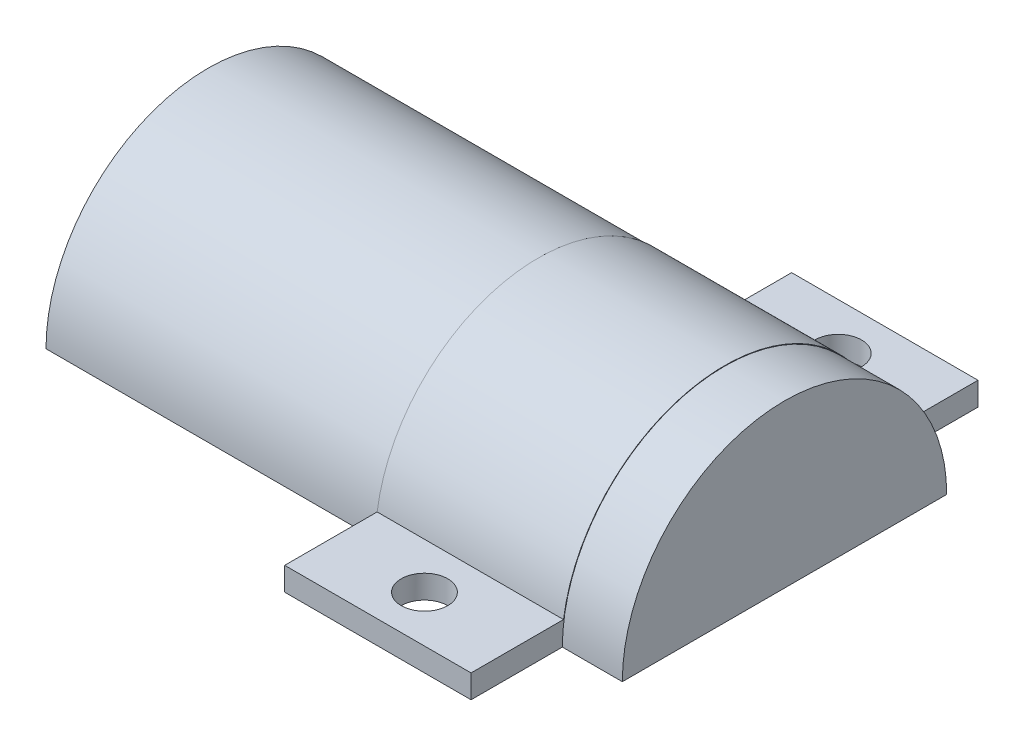
SolidWorks part; units mm, degrees
ref_plane "Front" through (0, 0, 0) normal (0, 0, 1) x (1, 0, 0)
ref_plane "Top" through (0, 0, 0) normal (0, 1, 0) x (1, 0, 0)
ref_plane "Right" through (0, 0, 0) normal (1, 0, 0) x (0, 0, -1)
sketch "Sketch1" plane through (0, 0, 0) normal (1, 0, 0) x (0, 0, -1)
  line L0 (-22.175, 0) -> (22.175, 0)
  line L1 (-22.175, 0) -> (-34.5465, 0)
  line L2 (-34.5465, 0) -> (-34.5465, 3.175)
  line L3 (-34.5465, 3.175) -> (-21.9465, 3.175)
  line L4 (0, 54.7215) -> (0, -65.0563) construction
  line L5 (22.175, 0) -> (34.5465, 0)
  line L6 (34.5465, 0) -> (34.5465, 3.175)
  line L7 (34.5465, 3.175) -> (21.9465, 3.175)
  circle A0 centre (0, 0) radius 19
  circle A1 centre (0, 0) radius 22.175
  dimension "D1" = 38
  dimension "D3" = 3.175
  dimension "D4" = 12.6
  dimension "D2" = 3.175
extrude "Boss-Extrude1" add sketch "Sketch1" along normal blind 25.4 contours A1 L3 L2 L1 | L4 A1 L0 A0 | A1 L4 A0 L0 | A1 L5 L6 L7
sketch "Sketch2" plane through (0, 3.175, 0) normal (0, 1, 0) x (1, 0, 0)
  line L0 (0, -34.5465) -> (0, -21.9465) construction
  line L2 (25.4, -34.5465) -> (0, -34.5465) construction
  circle A0 centre (12.7, -28.1965) radius 3.175
  dimension "D1" = 6.35
  dimension "D2" = 12.7
  dimension "D3" = 6.35
extrude "Cut-Extrude1" cut sketch "Sketch2" against normal blind 25.4
sketch "Sketch3" plane through (0, 3.175, 0) normal (0, 1, 0) x (1, 0, 0)
  line L0 (25.4, 34.5465) -> (25.4, 21.9465) construction
  line L1 (25.4, 34.5465) -> (0, 34.5465) construction
  circle A0 centre (12.7, 28.1965) radius 3.175
  dimension "D3" = 6.35
  dimension "D1" = 12.7
  dimension "D2" = 6.35
extrude "Cut-Extrude2" cut sketch "Sketch3" against normal blind 25.4
sketch "Sketch4" plane through (25.4, 0, 0) normal (1, 0, 0) x (0, 0, -1)
  line L0 (-19, 0) -> (-22.1047, 0)
  line L1 (22.1047, 0) -> (19, 0)
  circle A0 centre (0, 0) radius 18.9297
  circle A1 centre (0, 0) radius 22.1047
  line M1 (-34.5465, 0) -> (-19, 0)
  arc M2 (-19, 0) -> (19, 0) centre (0, 0) cw
  line M3 (19, 0) -> (34.5465, 0)
  arc M6 (21.9465, 3.175) -> (-21.9465, 3.175) centre (0, 0) ccw
  dimension "D1" = 3.175
extrude "Boss-Extrude2" add sketch "Sketch4" along normal blind 5 contours A1 M3 M6 M1 M2
sketch "Sketch5" plane through (30.4, 0, 0) normal (1, 0, 0) x (0, 0, -1)
  line L0 (-22.1491, 0) -> (22.1491, 0)
  circle A1 centre (0, 0) radius 22.1491
extrude "Boss-Extrude3" add sketch "Sketch5" along normal blind 3.175
sketch "Sketch6" plane through (0, 0, 0) normal (-1, 0, 0) x (0, 0, 1)
  line L0 (-22.1047, 0) -> (21.402, 0)
  line L1 (19, 0) -> (34.5465, 0) construction
  line L2 (21.402, 0) -> (22.0797, 0)
  circle A0 centre (0, 0) radius 22.0797
  circle A1 centre (0, 0) radius 18.9436
extrude "Boss-Extrude4" add sketch "Sketch6" along normal blind 45
